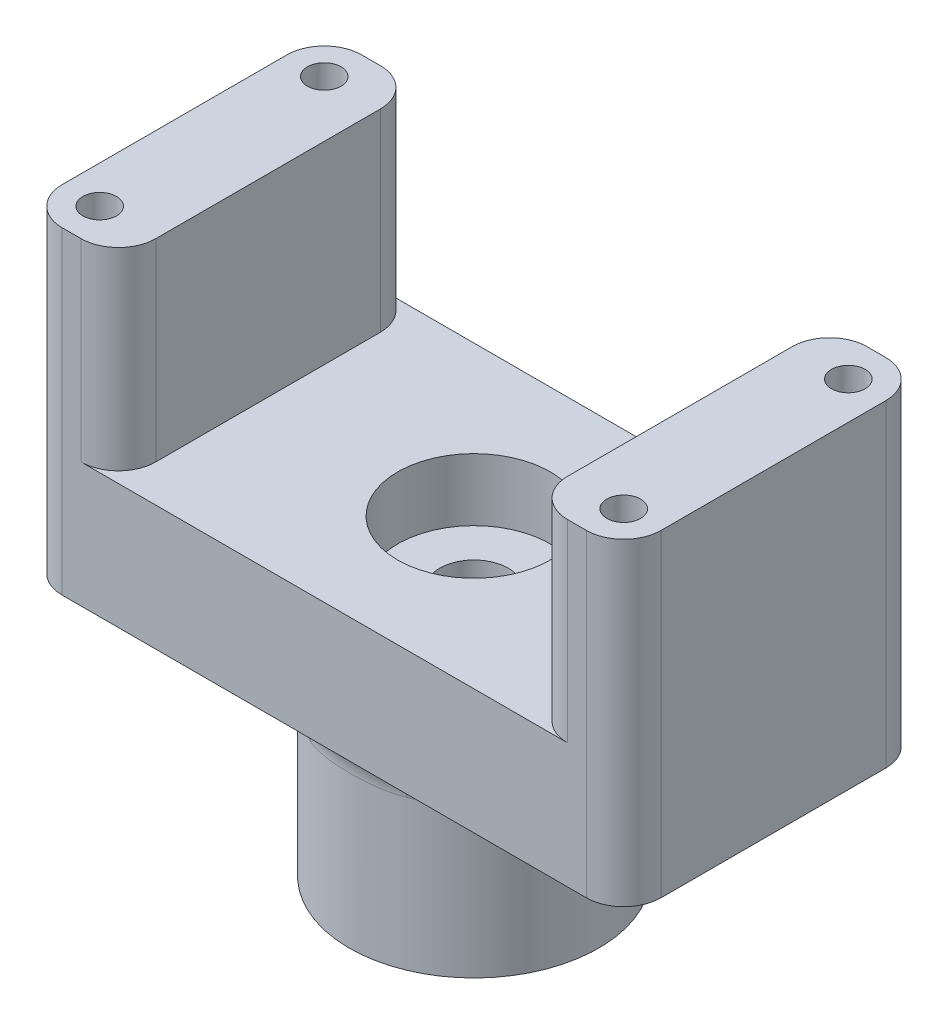
SolidWorks part; units mm, degrees
material "Nylon 101"
ref_plane "Front Plane" through (0, 0, 0) normal (0, 0, 1) x (1, 0, 0)
ref_plane "Top Plane" through (0, 0, 0) normal (0, 1, 0) x (1, 0, 0)
ref_plane "Right Plane" through (0, 0, 0) normal (1, 0, 0) x (0, 0, -1)
sketch "Sketch1" plane through (0, 0, 0) normal (0, 1, 0) x (1, 0, 0)
  line L0 (-21, -9) -> (21, 9) construction
  line L1 (19, 12) -> (16.5, 12)
  line L2 (16.5, 12) -> (16.5, -12)
  line L3 (16.5, -12) -> (19, -12)
  line L4 (0, -55) -> (0, 55) construction
  line L5 (-16.5, -12) -> (-19, -12)
  line L6 (-16.5, 12) -> (-16.5, -12)
  line L7 (-19, 12) -> (-16.5, 12)
  point P2 (0, 0)
  line B0 (-15.5, -16.5) -> (15.5, -16.5)
  line B1 (16.5, -15.5) -> (16.5, -14.5)
  line B2 (19, -12) -> (21, -12)
  line B3 (24, -9) -> (24, 9)
  line B4 (21, 12) -> (19, 12)
  line B5 (16.5, 14.5) -> (16.5, 15.5)
  line B6 (15.5, 16.5) -> (-15.5, 16.5)
  line B7 (-16.5, 15.5) -> (-16.5, 14.5)
  line B8 (-19, 12) -> (-21, 12)
  line B9 (-24, 9) -> (-24, -9)
  line B10 (-21, -12) -> (-19, -12)
  line B11 (-16.5, -14.5) -> (-16.5, -15.5)
  circle B12 centre (21, 9) radius 1.35
  circle B13 centre (-21, 9) radius 1.35
  circle B14 centre (21, -9) radius 1.35
  circle B15 centre (-21, -9) radius 1.35
  arc B16 (15.5, -16.5) -> (16.5, -15.5) centre (15.5, -15.5) ccw
  arc B17 (19, -12) -> (16.5, -14.5) centre (19, -14.5) ccw
  arc B18 (21, -12) -> (24, -9) centre (21, -9) ccw
  arc B19 (24, 9) -> (21, 12) centre (21, 9) ccw
  arc B20 (16.5, 14.5) -> (19, 12) centre (19, 14.5) ccw
  arc B21 (16.5, 15.5) -> (15.5, 16.5) centre (15.5, 15.5) ccw
  arc B22 (-15.5, 16.5) -> (-16.5, 15.5) centre (-15.5, 15.5) ccw
  arc B23 (-19, 12) -> (-16.5, 14.5) centre (-19, 14.5) ccw
  arc B24 (-21, 12) -> (-24, 9) centre (-21, 9) ccw
  arc B25 (-24, -9) -> (-21, -12) centre (-21, -9) ccw
  arc B26 (-16.5, -14.5) -> (-19, -12) centre (-19, -14.5) ccw
  arc B27 (-16.5, -15.5) -> (-15.5, -16.5) centre (-15.5, -15.5) ccw
sketch_block_instance "Block-piCAM-1"
sketch_block "Block-piCAM"
extrude "Boss-Extrude1" add sketch "Sketch1" along normal blind 15.5
sketch "Sketch2" plane through (0, 0, 0) normal (0, 1, 0) x (1, 0, 0)
  line L0 (24, 9) -> (24, -9) construction
  line L1 (21, -12) -> (16.5, -12) construction
  line L3 (16.5, 12) -> (21, 12) construction
  line L4 (-16.5, -12) -> (-21, -12) construction
  line L5 (-24, -9) -> (-24, 9) construction
  line L6 (-21, 12) -> (-16.5, 12) construction
  line L8 (24, 9) -> (24, -9)
  line L9 (21, -12) -> (16.5, -12)
  line L11 (16.5, 12) -> (21, 12)
  line L12 (-16.5, -12) -> (-21, -12)
  line L13 (-24, -9) -> (-24, 9)
  line L14 (-21, 12) -> (-16.5, 12)
  line L16 (-16.5, -12) -> (16.5, -12)
  line L17 (-16.5, 12) -> (16.5, 12)
  arc A0 (21, -12) -> (24, -9) centre (21, -9) ccw construction
  arc A1 (24, 9) -> (21, 12) centre (21, 9) ccw construction
  arc A2 (-24, -9) -> (-21, -12) centre (-21, -9) ccw construction
  arc A3 (-21, 12) -> (-24, 9) centre (-21, 9) ccw construction
  circle A4 centre (21, 9) radius 1.35 construction
  circle A5 centre (21, -9) radius 1.35 construction
  circle A6 centre (-21, 9) radius 1.35 construction
  circle A7 centre (-21, -9) radius 1.35 construction
  arc A8 (21, -12) -> (24, -9) centre (21, -9) ccw
  arc A9 (24, 9) -> (21, 12) centre (21, 9) ccw
  arc A10 (-24, -9) -> (-21, -12) centre (-21, -9) ccw
  arc A11 (-21, 12) -> (-24, 9) centre (-21, 9) ccw
  circle A12 centre (21, 9) radius 1.35
  circle A13 centre (21, -9) radius 1.35
  circle A14 centre (-21, 9) radius 1.35
  circle A15 centre (-21, -9) radius 1.35
extrude "Boss-Extrude2" add sketch "Sketch2" against normal blind 10
sketch "Sketch4" plane through (0, -10, 0) normal (0, -1, 0) x (1, 0, 0)
  circle A0 centre (0, 0) radius 10
  dimension "D1" = 20
extrude "Boss-Extrude3" add sketch "Sketch4" along normal blind 15
hole_wizard "CBORE for M5 Hex Head Bolt1" positions "3DSketch2" profile "Sketch3" counterbore size "M5" standard "ANSI Metric" end condition through all
sketch3d "3DSketch2"
  point P0 (0, 0, 0)
sketch "Sketch3" plane through (0, 0, 0) normal (1, 0, 0) x (0, 0, 1)
  line L0 (0, 0) -> (0, 25)
  line L1 (0, 25) -> (2.75, 25)
  line L3 (2.75, 25) -> (2.75, 5)
  line L4 (2.75, 5) -> (6.12, 5)
  line L5 (6.12, 5) -> (6.12, 0)
  line L7 (6.12, 0) -> (0, 0)
  line L11 (0, -6.35) -> (0, 107.95) construction
  dimension "Thru Hole Dia." = 5.5
  dimension "Thru Hole Depth" = 25
  dimension "C'Bore Dia." = 12.24
  dimension "C'Bore Depth" = 5
fillet "Fillet1" radius 3 5 edges at (16.5, 7.75, -12) (16.5, 7.75, 12) (-16.5, 7.75, -12) (-16.5, 7.75, 12) (0, -10, 10)
